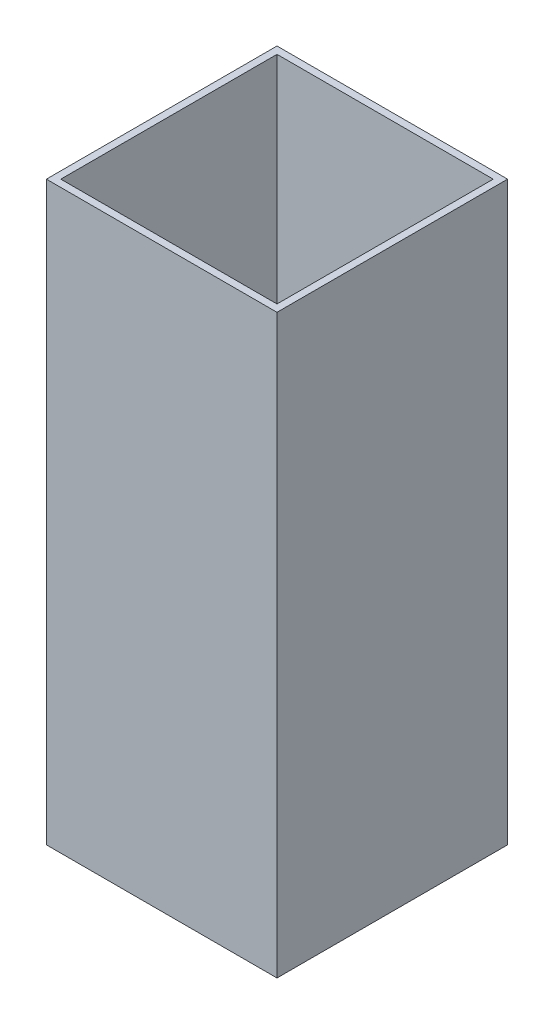
SolidWorks part; units mm, degrees
ref_plane "Front Plane" through (0, 0, 0) normal (0, 0, 1) x (1, 0, 0)
ref_plane "Top Plane" through (0, 0, 0) normal (0, 1, 0) x (1, 0, 0)
ref_plane "Right Plane" through (0, 0, 0) normal (1, 0, 0) x (0, 0, -1)
sketch "Sketch1" plane through (0, 0, 0) normal (0, 1, 0) x (1, 0, 0)
  line L0 (-16, 16) -> (-16, -16)
  line L1 (15, 15) -> (-15, 15)
  line L2 (15, 15) -> (15, -15)
  line L3 (15, -15) -> (-15, -15)
  line L4 (-15, 15) -> (-15, -15)
  line L5 (15, 15) -> (-15, -15) construction
  line L6 (15, -15) -> (-15, 15) construction
  line L7 (16, -16) -> (-16, -16)
  line L8 (16, 16) -> (16, -16)
  line L9 (16, 16) -> (-16, 16)
  point P0 (0, 0)
  dimension "D1" = 30
  dimension "D2" = 30
  dimension "D3" = 1
extrude "Boss-Extrude1" add sketch "Sketch1" along normal mid plane 80
